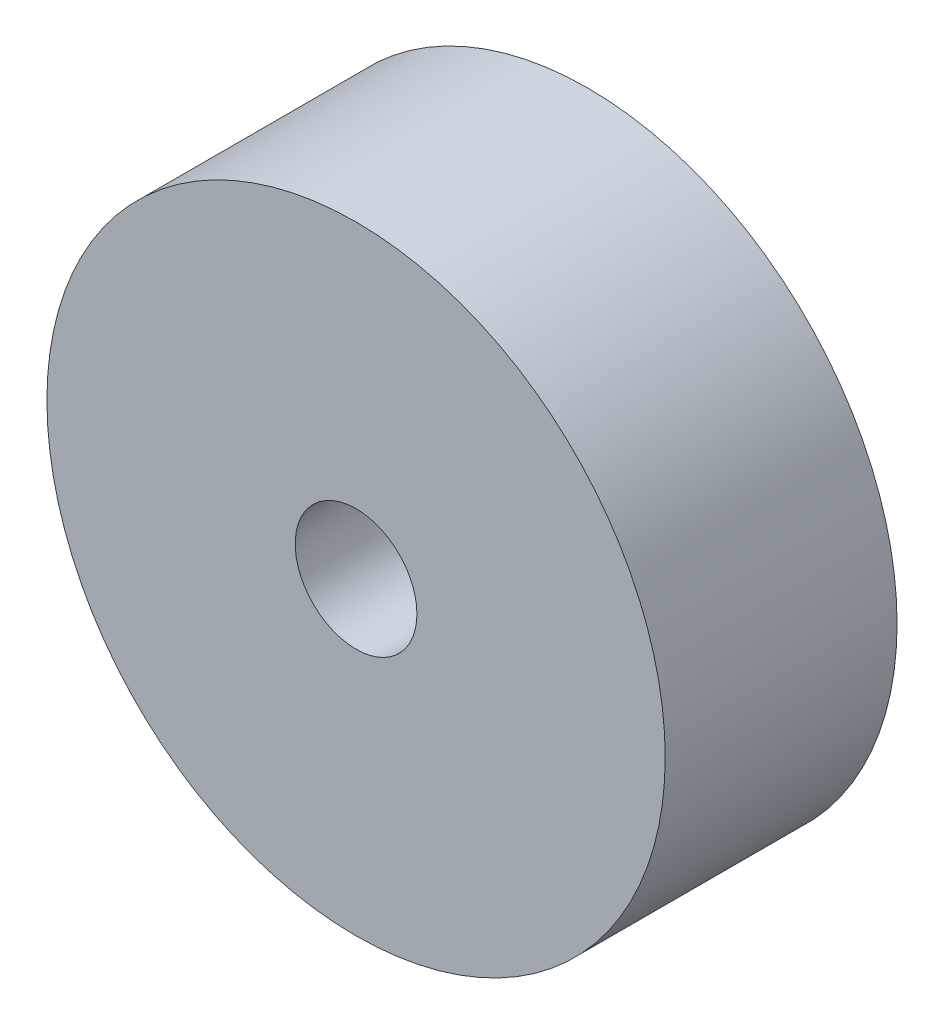
SolidWorks part; units mm, degrees
material "NEOPRENE"
ref_plane "Front Plane" through (0, 0, 0) normal (0, 0, 1) x (1, 0, 0)
ref_plane "Top Plane" through (0, 0, 0) normal (0, 1, 0) x (1, 0, 0)
ref_plane "Right Plane" through (0, 0, 0) normal (1, 0, 0) x (0, 0, -1)
sketch "Sketch1" plane through (0, 0, 0) normal (0, 0, 1) x (1, 0, 0)
  circle A0 centre (0, 0) radius 5
  circle A1 centre (0, 0) radius 25.4
  dimension "D1" = 10
  dimension "D2" = 50.8
extrude "Boss-Extrude1" add sketch "Sketch1" along normal mid plane 19.05
